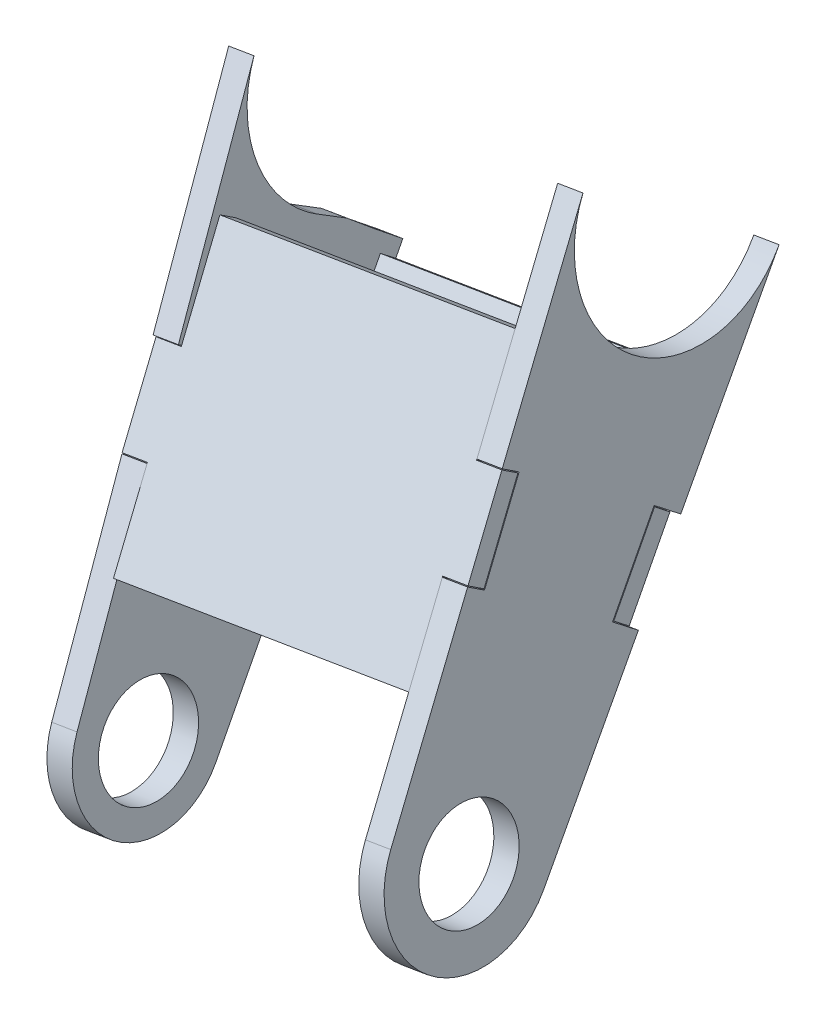
SolidWorks part; units mm, degrees
material "1.0545 (S355N)"
ref_plane "Płaszczyzna XY" through (0, 0, 0) normal (0, 0, 1) x (1, 0, 0)
ref_plane "Płaszczyzna XZ" through (0, 0, 0) normal (0, 1, 0) x (1, 0, 0)
ref_plane "Płaszczyzna YZ" through (0, 0, 0) normal (1, 0, 0) x (0, 0, -1)
ref_plane "Płaszczyzna1" through (1353.9262, 228.277, 3.4743) normal (-0.9861, -0.1663, -0.0025) x (-0.0025, -0.0004, 1)
sketch "Szkic1" plane through (1353.9262, 228.277, 3.4743) normal (-0.9861, -0.1663, -0.0025) x (-0.0025, -0.0004, 1)
  line L0 (441.2537, -472.7178) -> (412.3213, -422.3691)
  line L1 (426.7066, -482.3797) -> (391.5458, -436.223)
  circle A0 centre (433.6671, -477.0774) radius 5.75
  arc A1 (426.7066, -482.3797) -> (441.2537, -472.7178) centre (433.6671, -477.0774) ccw
  spline S1 degree 3 poles (412.3213, -422.3691) (419.5346, -434.9218) (409.3829, -443.0353) (398.9588, -440.8876) (396.245, -440.3285) (393.5495, -438.8533) (391.5458, -436.223) knots 0.155089 0.155089 0.155089 0.155089 0.5 0.5 0.5 0.636085 0.636085 0.636085 0.636085 weights 0.572065 0.397473 0.540118 1 0.818553 0.68649 0.603812
  dimension "D1" = 11.5
  dimension "D2" = 3
extrude "Dodanie-wyciągnięcie1" add sketch "Szkic1" along normal blind 3
sketch "Szkic2" plane through (1353.9262, 228.277, 3.4743) normal (-0.9861, -0.1663, -0.0025) x (-0.0025, -0.0004, 1)
  line L0 (404.6521, -441.2811) -> (407.8214, -439.4124)
  line L1 (391.5458, -436.223) -> (426.7066, -482.3797) construction
  line L2 (391.5458, -436.223) -> (398.9132, -445.8945)
  spline S1 degree 3 poles (404.6521, -441.2811) (402.8134, -442.8252) (400.8974, -444.367) (398.9132, -445.8945) knots 0 0 0 0 0.049967 0.049967 0.049967 0.049967 weights 1 0.976582 0.955504 0.936767
  spline S2 degree 3 poles (396.5878, -417.1047) (420.2566, -406.9902) (794.8831, -522.4609) (398.9588, -440.8876) (44.3046, -367.8173) (392.6219, -401.3146) (410.5, -419.9393) knots -0.227504 -0.227504 -0.227504 -0.227504 0.5 0.5 0.5 1.224974 1.224974 1.224974 1.224974 weights 2.32408 0.471355 0.029995 1 0.033369 0.468302 2.304799 only from (412.3213, -422.3691) to (391.5458, -436.223) construction
  spline S3 degree 3 poles (407.8214, -439.4124) (404.8882, -441.1419) (401.7438, -441.4614) (398.9588, -440.8876) (396.245, -440.3285) (393.5495, -438.8533) (391.5458, -436.223) knots 0.36101 0.36101 0.36101 0.36101 0.5 0.5 0.5 0.636085 0.636085 0.636085 0.636085 weights 0.598586 0.680875 0.81468 1 0.818553 0.68649 0.603812
extrude "Wytnij-wyciągnięcie2" cut sketch "Szkic2" along normal blind 4
ref_plane "Płaszczyzna2" through (1388.439, 234.096, 3.5629) normal (-0.9861, -0.1663, -0.0025) x (-0.0025, -0.0004, 1)
sketch "Szkic3" plane through (1388.439, 234.096, 3.5629) normal (-0.9861, -0.1663, -0.0025) x (-0.0025, -0.0004, 1)
  line L0 (441.9058, -471.8634) -> (411.6151, -424.0006)
  line L1 (425.9751, -483.0686) -> (391.1974, -438.4181)
  circle A0 centre (433.6671, -477.0774) radius 5.75
  arc A1 (425.9751, -483.0686) -> (441.9058, -471.8634) centre (433.6671, -477.0774) ccw
  circle A2 centre (433.6671, -477.0774) radius 9.75 construction
  spline S1 degree 3 poles (403.5827, -418.4452) (428.0684, -423.4901) (423.0142, -448.0212) (398.5285, -442.9763) (374.0428, -437.9315) (379.097, -413.4004) (403.5827, -418.4452) (428.0684, -423.4901) (423.0142, -448.0212) knots -0.5 0 0 0 0.5 0.5 0.5 1 1 1 1.5 1.5 1.5 weights 1 0.333333 0.333333 1 0.333333 0.333333 1 0.333333 0.333333 only from (403.5827, -418.4452) to (403.5827, -418.4452)
  dimension "D1" = 11.5
  dimension "D2" = 4
extrude "Dodanie-wyciągnięcie2" add sketch "Szkic3" against normal blind 3 separate body contours L0 S1 L1 A1 A0
sketch "Szkic4" plane through (1391.3972, 234.5948, 3.5705) normal (0.9861, 0.1663, 0.0025) x (0.0025, 0.0004, -1)
  line L0 (-433.6671, -477.0774) -> (-408.2523, -440.9445) construction
  line L1 (-418.31, -434.5793) -> (-408.2523, -440.9445) construction
  line L3 (-408.2523, -440.9445) -> (-398.862, -448.2585) construction
  line L5 (-441.9058, -471.8634) -> (-411.6151, -424.0006) construction
  line L6 (-425.9751, -483.0686) -> (-391.1974, -438.4181) construction
  spline S0 degree 3 poles (-411.6151, -424.0006) (-419.595, -436.6098) (-409.3023, -445.1961) (-398.5285, -442.9763) (-395.8541, -442.4253) (-393.1958, -440.9838) (-391.1974, -438.4181) knots 0.148934 0.148934 0.148934 0.148934 0.5 0.5 0.5 0.63446 0.63446 0.63446 0.63446 weights 0.581714 0.392484 0.531913 1 0.820719 0.689651 0.606795 construction
ref_plane "Płaszczyzna3" through (-11.0196, 63.801, 102.3043) normal (0.091, -0.527, -0.845) x (-0.1392, 0.8335, -0.5348)
sketch "Szkic5" plane through (-11.0196, 63.801, 102.3043) normal (0.091, -0.527, -0.845) x (-0.1392, 0.8335, -0.5348)
  line L0 (-635.4147, 1373.0399) -> (-577.398, 1373.0399) construction
  line L2 (-577.398, 1370.0399) -> (-635.4147, 1370.0399) construction
  line L4 (-578.3989, 1408.0399) -> (-635.0415, 1408.0399) construction
  line L6 (-635.0415, 1411.0399) -> (-578.3989, 1411.0399) construction
  line L8 (-622.2915, 1373.0399) -> (-612.2915, 1373.0399)
  line L10 (-602.2915, 1370.0399) -> (-612.2915, 1370.0399)
  line L12 (-590.9341, 1408.0399) -> (-602.2915, 1408.0399)
  line L14 (-612.2915, 1411.0399) -> (-602.2915, 1411.0399)
  line L16 (-602.2915, 1411.0399) -> (-602.2915, 1408.0399)
  line L17 (-602.2915, 1373.0399) -> (-602.2915, 1370.0399)
  line L18 (-612.2915, 1370.0399) -> (-612.2915, 1373.0399)
  line L19 (-612.2915, 1408.0399) -> (-612.2915, 1411.0399)
  line L20 (-590.9341, 1411.0399) -> (-590.9341, 1408.0399) construction
  line L21 (-629.2915, 1411.0399) -> (-629.2915, 1408.0399) construction
  line L24 (-590.9341, 1408.0399) -> (-590.9341, 1373.0399)
  line L25 (-622.2915, 1408.0399) -> (-622.2915, 1373.0399)
  line L26 (-612.2915, 1408.0399) -> (-622.2915, 1408.0399)
  line L27 (-602.2915, 1373.0399) -> (-590.9341, 1373.0399)
  dimension "D1" = 10
  dimension "D2" = 7
  dimension "D3" = 10
extrude "Dodanie-wyciągnięcie3" add sketch "Szkic5" along normal blind 2 separate body
sketch "Szkic6" plane through (1391.3972, 234.5948, 3.5705) normal (0.9861, 0.1663, 0.0025) x (0.0025, 0.0004, -1)
  line L1 (-429.8778, -452.6707) -> (-428.0188, -453.8472)
  line L2 (-428.0188, -453.8472) -> (-422.5642, -445.2282)
  line L3 (-422.5642, -445.2282) -> (-424.4231, -444.0517)
  line L4 (-424.3921, -444.1897) -> (-429.7398, -452.6397)
  line L5 (-429.7398, -452.6397) -> (-428.0498, -453.7092)
  line L6 (-428.0498, -453.7092) -> (-422.7021, -445.2593)
  line L7 (-422.7021, -445.2593) -> (-424.3921, -444.1897)
  line L10 (-428.0498, -453.7092) -> (-422.7021, -445.2593) construction
  line L14 (-430.5538, -452.2429) -> (-429.8778, -452.6707)
  line L15 (-427.8265, -447.9334) -> (-425.2915, -449.5377) construction
  line L16 (-424.4231, -444.0517) -> (-429.8778, -452.6707) construction
  line L17 (-424.3921, -444.1897) -> (-429.7398, -452.6397) construction
  line L18 (-429.7398, -452.6397) -> (-428.0498, -453.7092) construction
  line L19 (-422.7021, -445.2593) -> (-424.3921, -444.1897) construction
  line L20 (-430.5538, -452.2429) -> (-425.0991, -443.6239)
  line L21 (-425.0991, -443.6239) -> (-424.4231, -444.0517)
  dimension "D3" = 3
  dimension "D1" = 0
  dimension "D2" = 0.1
extrude "Wytnij-wyciągnięcie5" cut sketch "Szkic6" against normal through all
ref_plane "Płaszczyzna4" through (-4.8415, 28.1447, 37.4888) normal (0.1027, -0.5972, -0.7955) x (-0.9947, -0.0613, -0.0824)
sketch "Szkic8" plane through (-4.8415, 28.1447, 37.4888) normal (0.1027, -0.5972, -0.7955) x (-0.9947, -0.0613, -0.0824)
  line L0 (-1480.4592, -451.109) -> (-1472.996, -395.0101) construction
  line L1 (-1472.996, -395.0101) -> (-1475.9698, -394.6145) construction
  line L2 (-1475.9698, -394.6145) -> (-1483.433, -450.7134) construction
  line L5 (-1439.7026, -410.1559) -> (-1445.751, -455.6208) construction
  line L7 (-1442.7772, -456.0164) -> (-1436.7288, -410.5515) construction
  line L8 (-1478.764, -438.3665) -> (-1477.4452, -428.4539)
  line L9 (-1472.996, -395.0101) -> (-1475.9698, -394.6145)
  line L10 (-1479.1003, -418.1456) -> (-1480.419, -428.0583)
  line L13 (-1439.9307, -411.8706) -> (-1441.4322, -423.1568)
  line L15 (-1439.7771, -433.4651) -> (-1438.4584, -423.5524)
  line L16 (-1439.7771, -433.4651) -> (-1442.7509, -433.0695)
  line L17 (-1438.4584, -423.5524) -> (-1441.4322, -423.1568)
  line L18 (-1476.1265, -418.5412) -> (-1479.1003, -418.1456)
  line L19 (-1477.4452, -428.4539) -> (-1480.419, -428.0583)
  line L20 (-1444.9928, -449.921) -> (-1479.6871, -445.3054) construction
  line L21 (-1479.6871, -445.3054) -> (-1482.6609, -444.9098) construction
  line L22 (-1444.0696, -442.9821) -> (-1478.764, -438.3665)
  line L23 (-1442.7509, -433.0695) -> (-1444.0696, -442.9821)
  line L24 (-1439.9307, -411.8706) -> (-1474.625, -407.255)
  line L25 (-1476.1265, -418.5412) -> (-1474.625, -407.255)
  dimension "D1" = 10
  dimension "D2" = 7
  dimension "D3" = 10
extrude "Dodanie-wyciągnięcie4" add sketch "Szkic8" against normal blind 2 separate body contours L25 L18 L10 L19 L8 L22 L23 L16 L15 L17 L13 L24
sketch "Szkic9" plane through (1350.968, 227.7782, 3.4667) normal (-0.9861, -0.1663, -0.0025) x (-0.0025, -0.0004, 1)
  line L5 (412.9017, -464.4226) -> (414.6518, -463.0895)
  line L6 (414.6518, -463.0895) -> (408.4708, -454.9755)
  line L7 (408.4708, -454.9755) -> (406.7208, -456.3087)
  line L8 (406.8609, -456.3276) -> (412.9207, -464.2825)
  line L9 (412.9207, -464.2825) -> (414.5117, -463.0705)
  line L10 (414.5117, -463.0705) -> (408.4519, -455.1157)
  line L11 (408.4519, -455.1157) -> (406.8609, -456.3276)
  line L12 (406.8609, -456.3276) -> (412.9207, -464.2825) construction
  line L13 (412.9207, -464.2825) -> (414.5117, -463.0705) construction
  line L14 (414.5117, -463.0705) -> (408.4519, -455.1157) construction
  line L15 (408.4519, -455.1157) -> (406.8609, -456.3276) construction
  line L16 (411.5613, -459.0325) -> (408.3955, -461.4441) construction
  line L17 (406.7208, -456.3087) -> (412.9017, -464.4226) construction
  line L18 (412.9017, -464.4226) -> (411.4699, -465.5134)
  line L19 (411.4699, -465.5134) -> (405.2889, -457.3994)
  line L20 (406.7208, -456.3087) -> (405.2889, -457.3994)
  point P13 (408.3794, -461.4564)
  dimension "D3" = 4
  dimension "D1" = 0
  dimension "D2" = 0.1
extrude "Wytnij-wyciągnięcie6" cut sketch "Szkic9" against normal through all
